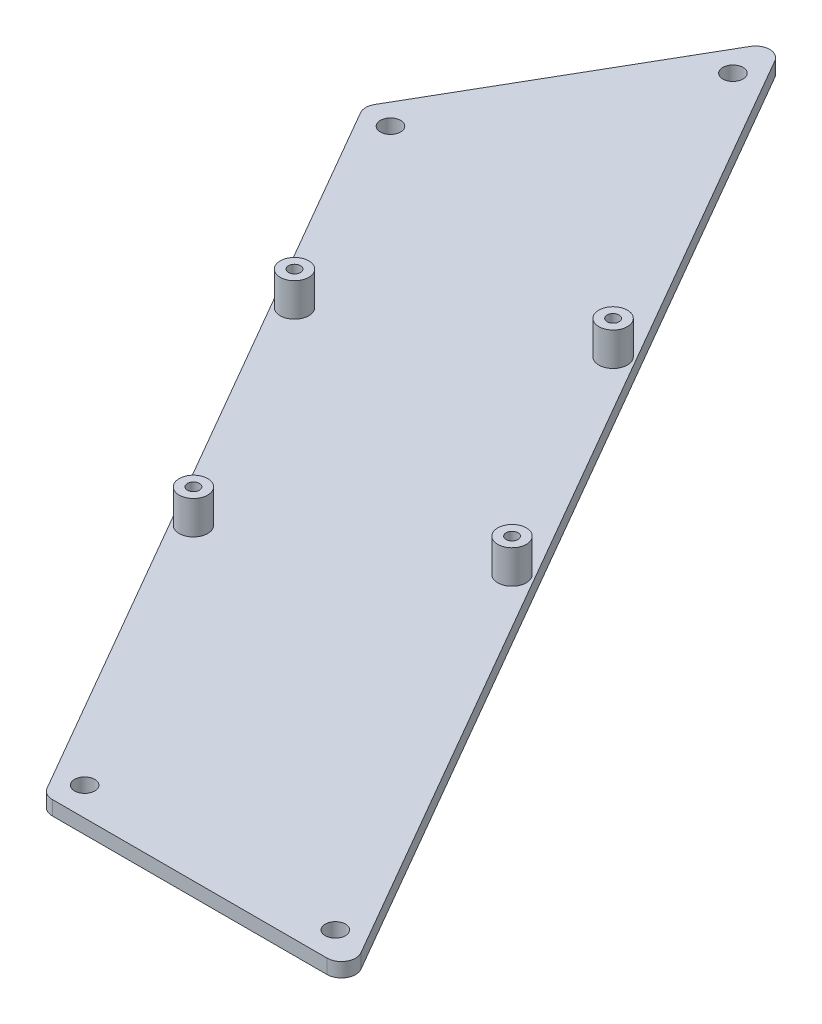
SolidWorks part; units mm, degrees
ref_plane "Front Plane" through (0, 0, 0) normal (0, 0, 1) x (1, 0, 0)
ref_plane "Top Plane" through (0, 0, 0) normal (0, 1, 0) x (1, 0, 0)
ref_plane "Right Plane" through (0, 0, 0) normal (1, 0, 0) x (0, 0, -1)
sketch "Sketch1" plane through (0, 0, 0) normal (0, 1, 0) x (1, 0, 0)
  line L9 (0, 0) -> (48, 0) construction
  line L10 (48, 0) -> (404, 0) construction
  line L11 (404, 0) -> (452, 0) construction
  line L12 (452, 0) -> (428, 41.5692) construction
  line L13 (428, 41.5692) -> (250, 349.8743) construction
  line L14 (250, 349.8743) -> (226, 391.4435) construction
  line L15 (226, 391.4435) -> (202, 349.8743) construction
  line L16 (202, 349.8743) -> (24, 41.5692) construction
  line L17 (24, 41.5692) -> (0, 0) construction
  line L18 (48, 0) -> (24, 41.5692) construction
  line L19 (202, 349.8743) -> (250, 349.8743) construction
  line L20 (428, 41.5692) -> (404, 0) construction
  line L22 (15.3397, 46.5692) -> (193.3397, 354.8743) construction
  line L28 (404, -10) -> (48, -10) construction
  line L30 (48, -10) -> (48, 10) construction
  line L31 (404, -10) -> (404, 10) construction
  line L32 (15.3397, 46.5692) -> (32.6603, 36.5692) construction
  line L33 (193.3397, 354.8743) -> (210.6603, 344.8743) construction
  line L34 (404, 10) -> (48, 10) construction
  line L35 (32.6603, 36.5692) -> (210.6603, 344.8743) construction
  line L51 (0, 0) -> (339, 195.7217) construction
  line L65 (81.3038, 152.8224) -> (113.6355, 208.8224)
  line L67 (48, -6) -> (404, -6) construction
  line L68 (81.3038, 152.8224) -> (173, -6)
  line L69 (173, -6) -> (237.6632, -6)
  line L70 (237.6632, -6) -> (113.6355, 208.8224)
  arc A0 (48, -10) -> (15.3397, 46.5692) centre (48, 27.7128) cw construction
  point P26 (175.6493, 101.4112)
  point P28 (127.1519, 73.4112)
  dimension "D1" = 356
  dimension "D2" = 48
  dimension "D3" = 10
  dimension "D4" = 16
  dimension "D5" = 125
  dimension "D6" = 56
extrude "Boss-Extrude1" add sketch "Sketch1" along normal blind 3
fillet "Fillet1" radius 3 4 edges at (81.3038, 1.5, -152.8224) (113.6355, 1.5, -208.8224) (173, 1.5, 6) (237.6632, 1.5, 6)
sketch "Sketch2" plane through (0, 3, 0) normal (0, 1, 0) x (1, 0, 0)
  line L0 (96.6036, 179.3224) -> (203.5996, -6) construction
  line L1 (111.0374, 204.3224) -> (82.1699, 154.3224) construction
  line L2 (174.7321, -6) -> (232.4671, -6) construction
  line L3 (127.1519, 73.4112) -> (175.6493, 101.4112) construction
  line L4 (82.1699, 151.3224) -> (172.134, -4.5) construction
  line L5 (235.0652, -1.5) -> (116.2335, 204.3224) construction
  line L6 (127.1519, 73.4112) -> (105.9019, 110.2173) construction
  line L7 (105.9019, 110.2173) -> (128.8516, 123.4673) construction
  line L8 (128.8516, 123.4673) -> (154.3993, 138.2173) construction
  line L9 (154.3993, 138.2173) -> (175.6493, 101.4112) construction
  line L10 (175.6493, 101.4112) -> (196.8993, 64.6051) construction
  line L11 (196.8993, 64.6051) -> (171.3516, 49.8551) construction
  line L12 (171.3516, 49.8551) -> (148.4019, 36.6051) construction
  line L13 (148.4019, 36.6051) -> (127.1519, 73.4112) construction
  line L14 (107.6519, 107.1862) -> (110.683, 108.9362) construction
  line L15 (110.683, 108.9362) -> (108.933, 111.9673) construction
  line L16 (110.683, 108.9362) -> (153.1183, 133.4362) construction
  line L17 (110.683, 108.9362) -> (139.683, 58.7067) construction
  line L18 (139.683, 58.7067) -> (182.1183, 83.2067) construction
  line L19 (182.1183, 83.2067) -> (153.1183, 133.4362) construction
  circle A0 centre (110.683, 108.9362) radius 3
  circle A1 centre (153.1183, 133.4362) radius 3
  circle A2 centre (182.1183, 83.2067) radius 3
  circle A3 centre (139.683, 58.7067) radius 3
  dimension "D3" = 6
  dimension "D1" = 85
  dimension "D2" = 3.5
  dimension "D4" = 49
  dimension "D5" = 58
extrude "Boss-Extrude2" add sketch "Sketch2" along normal blind 7
sketch "Sketch3" plane through (0, 10, 0) normal (0, 1, 0) x (1, 0, 0)
  circle A0 centre (110.683, 108.9362) radius 1.25
  circle A1 centre (153.1183, 133.4362) radius 1.25
  circle A2 centre (182.1183, 83.2067) radius 1.25
  circle A3 centre (139.683, 58.7067) radius 1.25
  circle A4 centre (153.1183, 133.4362) radius 3 construction
  circle A5 centre (110.683, 108.9362) radius 3 construction
  circle A6 centre (139.683, 58.7067) radius 3 construction
  circle A7 centre (182.1183, 83.2067) radius 3 construction
  dimension "D1" = 2.5
extrude "Cut-Extrude1" cut sketch "Sketch3" against normal through all
sketch "Sketch4" plane through (0, 3, 0) normal (0, 1, 0) x (1, 0, 0)
  line L0 (84.7679, 146.8224) -> (117.0996, 202.8224) construction
  line L1 (82.1699, 151.3224) -> (172.134, -4.5) construction
  line L2 (235.0652, -1.5) -> (116.2335, 204.3224) construction
  line L3 (169.5359, 0) -> (234.1991, 0) construction
  line L4 (174.7321, -6) -> (232.4671, -6) construction
  line L5 (111.0374, 204.3224) -> (82.1699, 154.3224) construction
  circle A0 centre (87.7679, 152.0185) radius 2.125
  circle A1 centre (114.0996, 197.6262) radius 2.125
  circle A2 centre (175.5359, 0) radius 2.125
  circle A3 centre (228.1991, 0) radius 2.125
  dimension "D3" = 4.25
  dimension "D1" = 6
  dimension "D2" = 6
  dimension "D4" = 6
  dimension "D5" = 6
  dimension "D6" = 6
  dimension "D7" = 6
extrude "Cut-Extrude2" cut sketch "Sketch4" against normal through all
